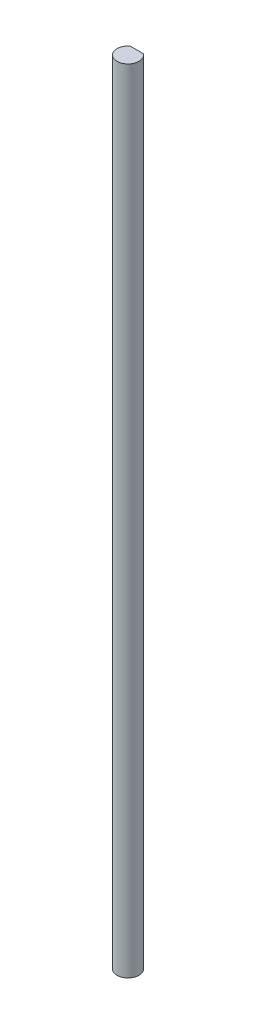
SolidWorks part; units mm, degrees
ref_plane "Front Plane" through (0, 0, 0) normal (0, 0, 1) x (1, 0, 0)
ref_plane "Top Plane" through (0, 0, 0) normal (0, 1, 0) x (1, 0, 0)
ref_plane "Right Plane" through (0, 0, 0) normal (1, 0, 0) x (0, 0, -1)
sketch "Sketch1" plane through (0, 0, 0) normal (0, 1, 0) x (1, 0, 0)
  line L0 (-1.905, 2.54) -> (1.905, 2.54)
  arc A0 (-1.905, 2.54) -> (1.905, 2.54) centre (0, 0) ccw
  dimension "D1" = 6.35
  dimension "D2" = 2.54
extrude "Boss-Extrude1" add sketch "Sketch1" along normal blind 228.6
